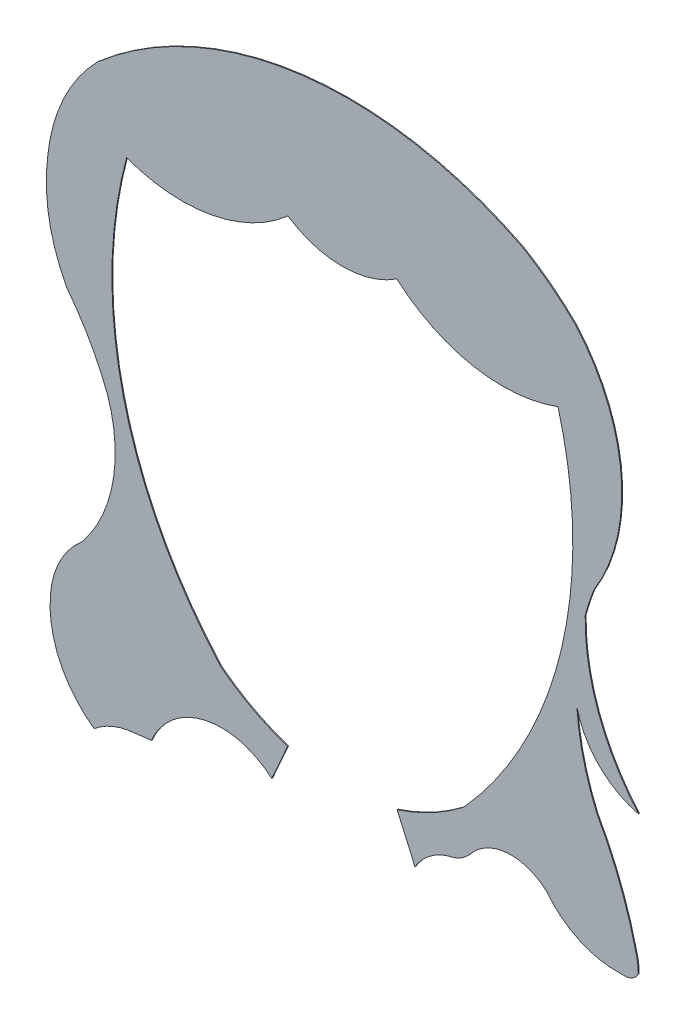
SolidWorks part; units mm, degrees
ref_plane "Alzado" through (0, 0, 0) normal (0, 0, 1) x (1, 0, 0)
ref_plane "Planta" through (0, 0, 0) normal (0, 1, 0) x (1, 0, 0)
ref_plane "Vista lateral" through (0, 0, 0) normal (1, 0, 0) x (0, 0, -1)
sketch "Model" plane through (0, 0, 0) normal (0, 0, 1) x (1, 0, 0)
  line L0 (7.8426, 33.9514) -> (9.5797, 37.8569)
  line L1 (-5.3348, 30.9793) -> (-7.9291, 30.6615)
  line L2 (21.5603, 37.8557) -> (23.2969, 33.9511)
  arc A0 (47.9622, 35.5076) -> (47.6116, 37.74) centre (40.0763, 35.4127) ccw
  arc A1 (-16.3838, 39.212) -> (-11.5931, 28.9583) centre (-5.0207, 38.2751) ccw
  arc A2 (-12.9464, 45.9809) -> (-16.3838, 39.212) centre (-6.7013, 38.5522) ccw
  arc A3 (-12.9464, 45.9809) -> (-10.129, 61.3532) centre (-25.449, 56.2167) ccw
  arc A4 (-10.129, 61.3532) -> (-14.6011, 69.2719) centre (-39.1224, 50.2014) ccw
  arc A5 (-16.6742, 80.7012) -> (-14.6011, 69.2719) centre (2.184, 78.2191) ccw
  arc A6 (-11.2426, 92.3313) -> (-16.6742, 80.7012) centre (2.6041, 78.781) ccw
  arc A7 (35.3223, 98.018) -> (-11.2426, 92.3313) centre (16.2651, 60.5774) ccw
  arc A8 (7.8426, 33.9514) -> (-5.3348, 30.9793) centre (2.3394, 27.6527) ccw
  arc A9 (46.4374, 34.556) -> (45.9789, 34.555) centre (46.2213, 28.5599) ccw
  arc A10 (37.931, 38.2775) -> (45.9789, 34.555) centre (45.5862, 44.2667) ccw
  arc A11 (37.931, 38.2775) -> (29.5943, 37.6834) centre (34.0416, 34.0661) ccw
  arc A12 (27.332, 36.2968) -> (29.5943, 37.6834) centre (26.4911, 40.2074) ccw
  arc A13 (27.332, 36.2968) -> (26.7957, 36.1416) centre (28.1729, 32.3861) ccw
  arc A14 (26.7957, 36.1416) -> (23.5037, 33.3986) centre (28.9878, 30.1639) ccw
  arc A15 (46.4374, 34.556) -> (47.9622, 35.5076) centre (46.4953, 36.1607) ccw
  arc A16 (21.5603, 37.8557) -> (28.7023, 41.6228) centre (14.1065, 60.6412) ccw
  arc A17 (2.4465, 41.6182) -> (9.5797, 37.8569) centre (17.0356, 60.6417) ccw
  arc A18 (-8.0399, 84.8595) -> (9.6038, 88.1504) centre (-1.9711, 101.2654) ccw
  arc A19 (9.6038, 88.1504) -> (21.5353, 88.1505) centre (15.5695, 97.1403) ccw
  arc A20 (21.5353, 88.1505) -> (39.1791, 84.8599) centre (33.11, 101.2657) ccw
  arc A21 (28.9729, 41.8734) -> (39.1791, 84.8599) centre (-5.4161, 72.7431) ccw
  arc A22 (28.7023, 41.6228) -> (28.9729, 41.8734) centre (27.4846, 43.2094) ccw
  arc A23 (2.1757, 41.8687) -> (2.4465, 41.6182) centre (3.6636, 43.2052) ccw
  arc A24 (-8.0399, 84.8595) -> (2.1757, 41.8687) centre (36.5566, 72.7475) ccw
  arc A25 (42.149, 66.5873) -> (48.0017, 50.6598) centre (65.7276, 66.2124) ccw
  arc A26 (43.1212, 69.4876) -> (42.149, 66.5873) centre (68.6268, 59.325) ccw
  arc A27 (43.1212, 69.4876) -> (41.1131, 93.552) centre (25.8588, 80.1631) ccw
  arc A28 (41.1131, 93.552) -> (35.3223, 98.018) centre (20.3821, 72.6591) ccw
  arc A29 (47.6116, 37.74) -> (43.4311, 48.4169) centre (6.8421, 27.9336) ccw
  arc A30 (41.2342, 57.4649) -> (43.4311, 48.4169) centre (68.6268, 59.325) ccw
  arc A31 (41.2342, 57.4649) -> (48.0017, 50.6598) centre (50.135, 59.5489) ccw
  arc A32 (-7.9291, 30.6615) -> (-11.5931, 28.9583) centre (-6.5544, 22.9115) ccw
  arc A33 (23.2969, 33.9511) -> (23.5037, 33.3986) centre (25.2529, 34.3683) ccw
extrude "Saliente-Extruir1" add sketch "Model" along normal blind 0.1
